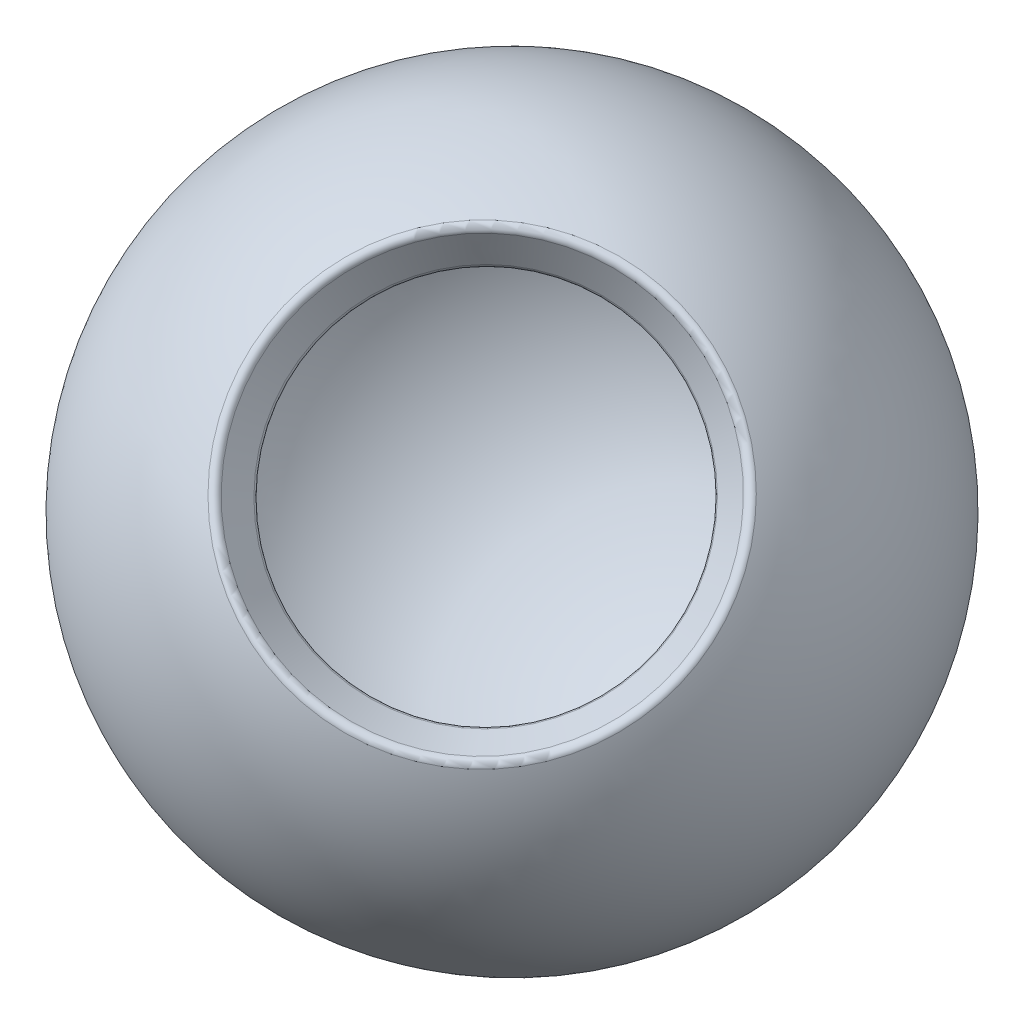
SolidWorks part; units mm, degrees
other "Camera2"
other "Camera3"
ref_plane "Front Plane" through (0, 0, 0) normal (0, 0, 1) x (1, 0, 0)
ref_plane "Top Plane" through (0, 0, 0) normal (0, 1, 0) x (1, 0, 0)
ref_plane "Right Plane" through (0, 0, 0) normal (1, 0, 0) x (0, 0, -1)
sketch "Sketch1" plane through (0, 0, 0) normal (1, 0, 0) x (0, 0, -1)
  line L0 (0, 75.5838) -> (0, -74.0752) construction
  line L1 (-72.8442, 103.278) -> (-61.9176, 87.6732)
  line L2 (0, -108.7043) -> (0, -127.7543)
  arc A0 (-72.8442, 103.278) -> (0, -127.7543) centre (0, -0.7543) ccw
  arc A1 (-61.9176, 87.6732) -> (0, -108.7043) centre (0, -0.7543) ccw
  dimension "D1" = 254
  dimension "D2" = 215.9
  dimension "D5" = 35
revolve "Revolve5" add sketch "Sketch1" angle 360 about L0
fillet "Fillet1" radius 2.54 2 edges at (0, 87.6732, 61.9176) (0, 103.278, 72.8442)
sketch "Sketch3" plane through (0, 0, 0) normal (0, 1, 0) x (1, 0, 0)
  line L0 (0, 100.2856) -> (0, -139.8494) construction
  line L1 (103.371, 0) -> (-151.8036, 0) construction
sketch "Sketch4" plane through (0, 0, 0) normal (1, 0, 0) x (0, 0, -1)
  line L0 (93.4541, 0) -> (-240.0587, -188.8529)
  line L1 (100.2856, 0) -> (-139.8494, 0) construction
ref_plane "Plane4" through (-21.352, -12.539, -7.1003) normal (0.8289, 0.4868, 0.2756) x (0.5594, -0.7213, -0.4084)
ref_plane "Plane5" through (0, -127.7543, 0) normal (0, -1, 0) x (1, 0, 0)
ref_plane "Plane6" through (0, 0, 0) normal (0, 0.7193, -0.6947) x (1, 0, 0)
ref_plane "Plane7" through (0, -92.2213, 89.057) normal (0, 0.7193, -0.6947) x (-1, 0, 0)
sketch "Sketch6" plane through (0, -92.2213, 89.057) normal (0, 0.7193, -0.6947) x (-1, 0, 0)
  line L1 (-406.0275, 232.9419) -> (502.8615, 232.9419)
  line L2 (-406.0275, 232.9419) -> (-406.0275, -350.205)
  line L3 (-406.0275, -350.205) -> (502.8615, -350.205)
  line L4 (502.8615, 232.9419) -> (502.8615, -350.205)
extrude "Boss-Extrude1" [suppressed] add sketch "Sketch6" along normal blind 2.54 separate body
sketch "Sketch7" plane through (0, -92.2213, 89.057) normal (0, 0.7193, -0.6947) x (-1, 0, 0)
  line L0 (-133.7942, 0) -> (153.0763, 0)
ref_plane "Decal axis plane" through (0, 0, 0) normal (0, -0.6947, -0.7193) x (-1, 0, 0)
sketch "Decal Axis" plane through (0, 0, 0) normal (0, -0.6947, -0.7193) x (-1, 0, 0)
  line L0 (0, 115.7925) -> (0, -79.5161) construction
move or copy body "Body-Move/Copy1" bodies to move or copy 101 copy no rotation origin (2.292, -12.1334, -1.4827) rotation axis (0.8192, 0.2195, -0.5299) rotation angle 53.647
